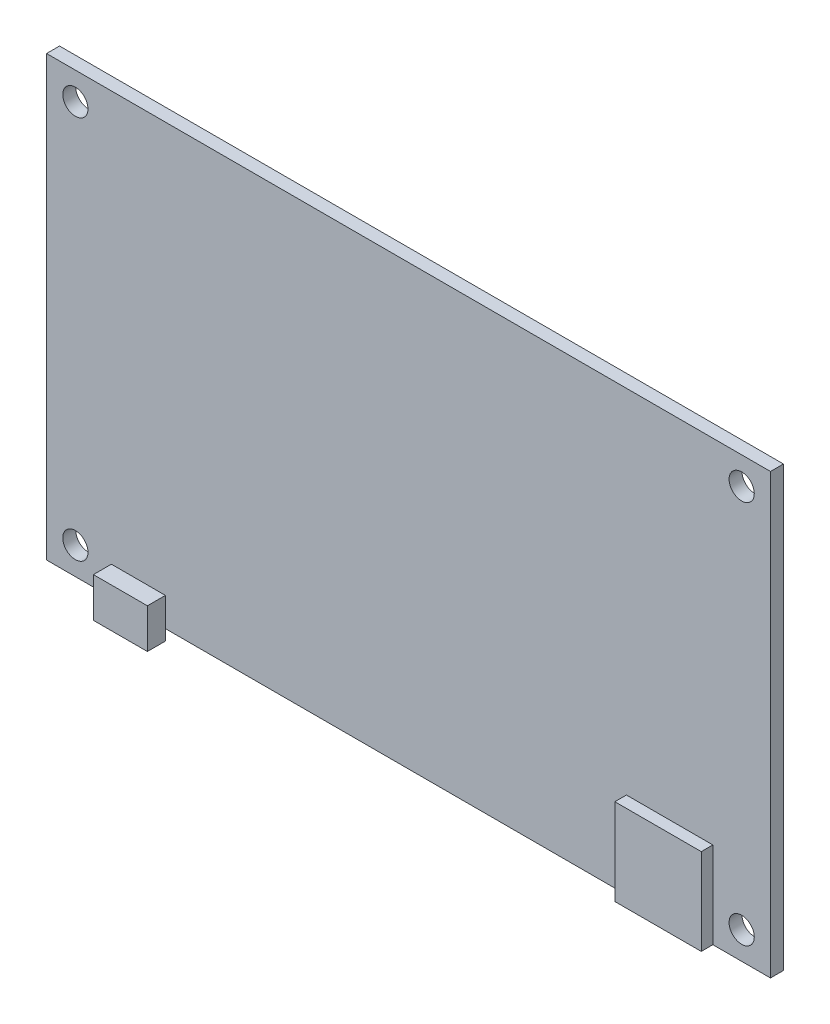
SolidWorks part; units mm, degrees
ref_plane "Front" through (0, 0, 0) normal (0, 0, 1) x (1, 0, 0)
ref_plane "Top" through (0, 0, 0) normal (0, 1, 0) x (1, 0, 0)
ref_plane "Right" through (0, 0, 0) normal (1, 0, 0) x (0, 0, -1)
sketch "Sketch1" plane through (0, 0, 0) normal (0, 0, 1) x (1, 0, 0)
  line L1 (-50.25, 60.9) -> (50.25, 60.9)
  line L2 (-50.25, 60.9) -> (-50.25, 0)
  line L3 (-50.25, 0) -> (50.25, 0)
  line L4 (50.25, 60.9) -> (50.25, 0)
  dimension "D1" = 60.9
  dimension "D2" = 100.5
extrude "Boss-Extrude1" add sketch "Sketch1" along normal blind 1.8
sketch "Sketch2" plane through (0, 0, 1.8) normal (0, 0, 1) x (1, 0, 0)
  line L0 (-50.25, 0) -> (50.25, 0) construction
  line L1 (-50.25, 30.45) -> (50.25, 30.45) construction
  line L2 (-50.25, 60.9) -> (-50.25, 0) construction
  line L3 (50.25, 0) -> (50.25, 60.9) construction
  circle A0 centre (-46.25, 3.8) radius 1.75
  circle A1 centre (-46.25, 57.1) radius 1.75
  dimension "D2" = 3.5
  dimension "D1" = 46.25
  dimension "D3" = 3.8
extrude "Cut-Extrude1" cut sketch "Sketch2" against normal up to next (1.8 mm away)
mirror "Mirror1" about plane through (0, 0, 0) normal (1, 0, 0) of "Cut-Extrude1"
sketch "Sketch3" plane through (0, 0, 1.8) normal (0, 0, 1) x (1, 0, 0)
  line L0 (-50.25, 0) -> (50.25, 0) construction
  line L1 (30.25, 0) -> (42.25, 0)
  line L2 (30.25, 0) -> (30.25, 12)
  line L3 (30.25, 12) -> (42.25, 12)
  line L4 (42.25, 0) -> (42.25, 12)
  line L5 (50.25, 0) -> (50.25, 60.9) construction
  dimension "D1" = 12
  dimension "D2" = 8
extrude "Boss-Extrude2" add sketch "Sketch3" along normal offset from surface (1.61 mm away) 3.41 up to face at (48, 3.8, 0)
sketch "Sketch4" plane through (0, 0, 1.8) normal (0, 0, 1) x (1, 0, 0)
  line L1 (-41.25, -1.5) -> (-33.75, -1.5)
  line L2 (-41.25, -1.5) -> (-41.25, 4)
  line L3 (-41.25, 4) -> (-33.75, 4)
  line L4 (-33.75, -1.5) -> (-33.75, 4)
  line L5 (-50.25, 0) -> (30.25, 0) construction
  line L6 (-50.25, 60.9) -> (-50.25, 0) construction
  dimension "D1" = 7.5
  dimension "D2" = 1.5
  dimension "D3" = 5.5
  dimension "D4" = 9
extrude "Boss-Extrude3" add sketch "Sketch4" along normal offset from surface (2.5 mm away) 4.3 up to face at (48, 3.8, 0)
sketch "Esboço1" plane through (0, 0, 0) normal (0, 0, -1) x (-1, 0, 0)
  line L0 (-50.25, 0) -> (-50.25, 60.9) construction
  line L1 (-56.25, 80.9) -> (56.25, 80.9)
  line L2 (-56.25, 80.9) -> (-56.25, -6)
  line L3 (-56.25, -6) -> (56.25, -6)
  line L4 (56.25, 80.9) -> (56.25, -6)
  line L5 (-50.25, 60.9) -> (50.25, 60.9) construction
  line L6 (50.25, 60.9) -> (50.25, 0) construction
  line L7 (50.25, 0) -> (-50.25, 0) construction
  line L8 (53.25, 77.9) -> (53.25, -3) construction
  line L9 (53.25, 74.9) -> (53.25, -3)
  line L10 (-53.25, -3) -> (53.25, -3)
  line L11 (-53.25, 74.9) -> (-53.25, -3)
  line L12 (-53.25, 74.9) -> (53.25, 74.9)
  line L13 (-53.25, 77.9) -> (-53.25, -3) construction
  line L14 (-53.25, 77.9) -> (53.25, 77.9) construction
  dimension "D1" = 6
  dimension "D2" = 20
  dimension "D3" = 6
  dimension "D4" = 6
  dimension "D6" = 6
  dimension "D5" = 3
extrude "Ressalto-extrusão1" [suppressed] add sketch "Esboço1" against normal blind 25 separate body
sketch "Esboço2" [suppressed] plane through (0, 0, 0) normal (0, 0, -1) x (-1, 0, 0)
  line L0 (56.25, -6) -> (56.25, 80.9) construction
  line L1 (-56.25, 80.9) -> (56.25, 80.9)
  line L2 (-56.25, 80.9) -> (-56.25, -6)
  line L3 (-56.25, -6) -> (56.25, -6)
  line L4 (56.25, 80.9) -> (56.25, -6)
extrude "Ressalto-extrusão2" [suppressed] add sketch "Esboço2" along normal blind 3
sketch "Esboço3" [suppressed] plane through (0, 80.9, 0) normal (0, 1, 0) x (1, 0, 0)
  circle A0 centre (41.25, -12) radius 9.0612
  circle A1 centre (-41.25, -12) radius 10.1478
hole_wizard "Rebaixo para parafuso com cabeça panela de M31" [suppressed] positions "Esboço5" profile "Esboço4" counterbore size "M3" standard "ISO"
sketch "Esboço5" [suppressed] plane through (0, 74.9, 0) normal (0, 1, 0) x (1, 0, 0)
  point P0 (41.25, -12)
  point P2 (-41.25, -12)
sketch "Esboço4" plane through (41.25, 74.9, 12) normal (1, 0, 0) x (0, 0, -1)
  line L0 (0, 0) -> (0, 6)
  line L1 (0, 6) -> (1.7, 6)
  line L3 (1.7, 6) -> (1.7, 2.4)
  line L4 (1.7, 2.4) -> (3.5, 2.4)
  line L5 (3.5, 2.4) -> (3.5, 0)
  line L7 (3.5, 0) -> (0, 0)
  line L11 (0, -6.35) -> (0, 107.95) construction
  dimension "Thru Hole Dia." = 3.4
  dimension "Thru Hole Depth" = 6
  dimension "C'Bore Dia." = 7
  dimension "C'Bore Depth" = 2.4
sketch "Esboço6" [suppressed] plane through (0, -6, 0) normal (0, -1, 0) x (1, 0, 0)
  circle A0 centre (41.25, 12) radius 3.5
  circle A1 centre (-41.25, 12) radius 3.5
  dimension "D1" = 7
extrude "Corte-extrusão1" [suppressed] cut sketch "Esboço6" against normal blind 10
hole_wizard "Broca de rosquear para tarraxa de M31" [suppressed] positions "Esboço8" profile "Esboço7" hole size "M3" standard "ISO"
sketch "Esboço8" [suppressed] plane through (0, 0, -3) normal (0, 0, -1) x (-1, 0, 0)
  point P0 (-46.25, 57.1)
  point P3 (46.25, 57.1)
  point P5 (-46.25, 3.8)
  point P7 (46.25, 3.8)
  point P9 (-46.25, 57.1)
sketch "Esboço7" plane through (46.25, 57.1, -3) normal (1, 0, 0) x (0, 1, 0)
  line L0 (0, 0) -> (0, 28)
  line L1 (0, 28) -> (1.25, 28)
  line L2 (1.25, 28) -> (1.25, 0)
  line L5 (1.25, 0) -> (0, 0)
  line L11 (0, -6.35) -> (0, 107.95) construction
  dimension "Thru Hole Dia." = 2.5
  dimension "Thru Hole Depth" = 28
